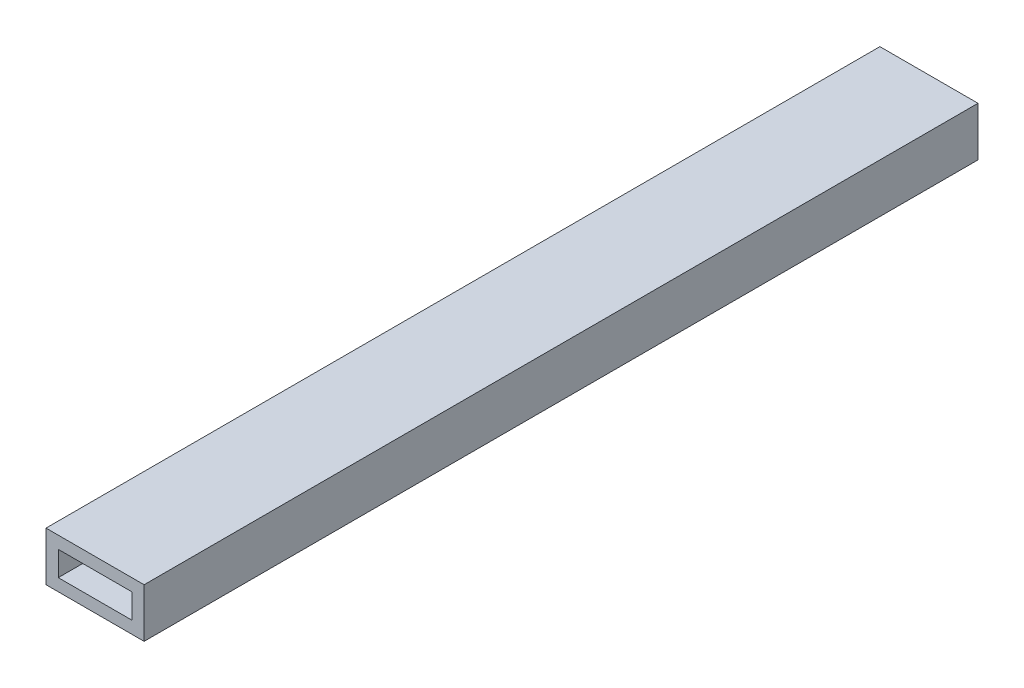
SolidWorks part; units mm, degrees
ref_plane "Front" through (0, 0, 0) normal (0, 0, 1) x (1, 0, 0)
ref_plane "Top" through (0, 0, 0) normal (0, 1, 0) x (1, 0, 0)
ref_plane "Right" through (0, 0, 0) normal (1, 0, 0) x (0, 0, -1)
sketch "Sketch1" plane through (0, 0, 0) normal (0, 0, 1) x (1, 0, 0)
  line L1 (-10.4248, 8.0668) -> (14.9752, 8.0668)
  line L2 (-10.4248, 8.0668) -> (-10.4248, -4.6332)
  line L3 (-10.4248, -4.6332) -> (14.9752, -4.6332)
  line L4 (14.9752, 8.0668) -> (14.9752, -4.6332)
  dimension "D1" = 25.4
  dimension "D2" = 12.7
extrude "Boss-Extrude1" add sketch "Sketch1" along normal blind 215.9 contours L1 L4 L3 L2
sketch "Sketch3" plane through (0, 0, 0) normal (0, 0, -1) x (-1, 0, 0)
  line L8 (7.2498, -1.4582) -> (7.2498, 4.8918)
  line L9 (7.2498, 4.8918) -> (-11.8002, 4.8918)
  line L10 (-11.8002, 4.8918) -> (-11.8002, -1.4582)
  line L11 (-11.8002, -1.4582) -> (7.2498, -1.4582)
  line L12 (7.2498, -1.4582) -> (7.2498, 4.8918)
  line L13 (7.2498, 4.8918) -> (-11.8002, 4.8918)
  line L14 (-11.8002, 4.8918) -> (-11.8002, -1.4582)
  line L15 (-11.8002, -1.4582) -> (7.2498, -1.4582)
  dimension "D1" = 3.175
extrude "Cut-Extrude1" cut sketch "Sketch3" against normal through all
